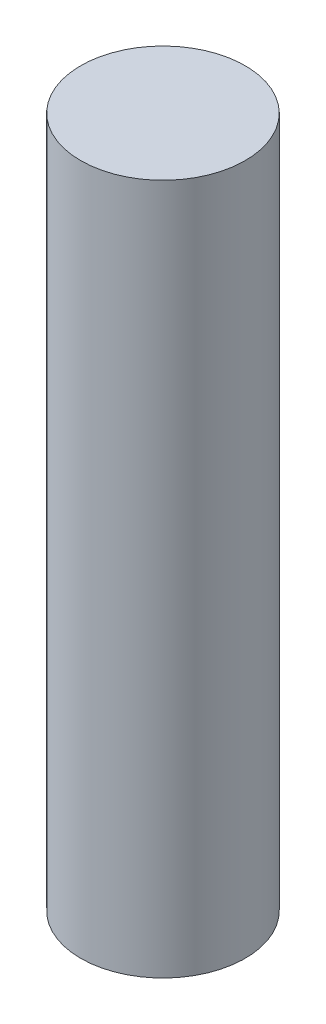
SolidWorks part; units mm, degrees
ref_plane "Front Plane" through (0, 0, 0) normal (0, 0, 1) x (1, 0, 0)
ref_plane "Top Plane" through (0, 0, 0) normal (0, 1, 0) x (1, 0, 0)
ref_plane "Right Plane" through (0, 0, 0) normal (1, 0, 0) x (0, 0, -1)
sketch "Sketch1" plane through (0, 0, 0) normal (0, 1, 0) x (1, 0, 0)
  circle A0 centre (0, 0) radius 1.25
  dimension "D1" = 2.5
extrude "Boss-Extrude1" add sketch "Sketch1" along normal blind 10.5
